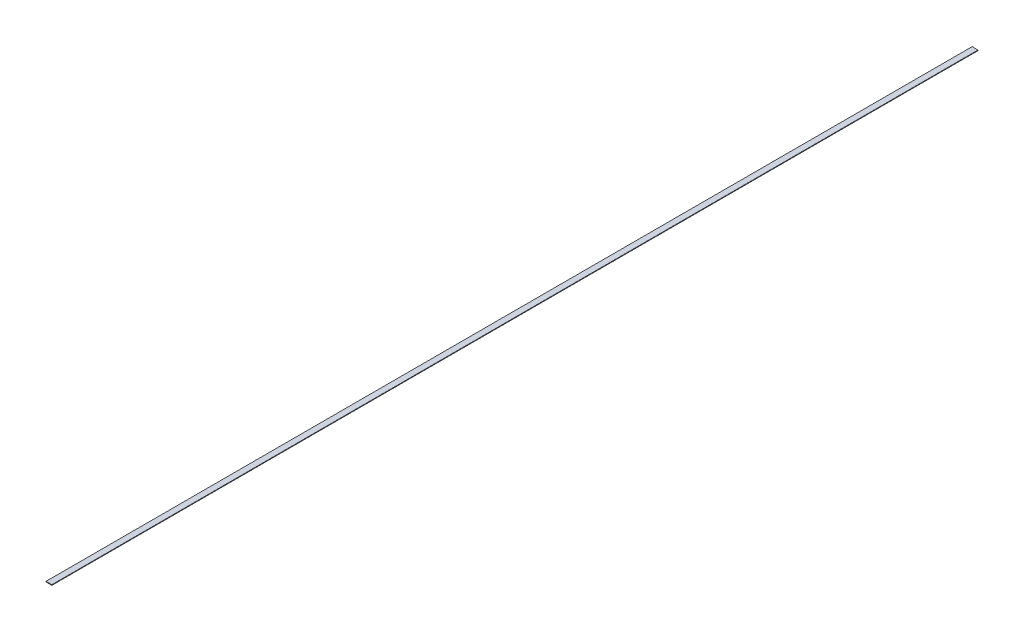
SolidWorks part; units mm, degrees
ref_plane "Front Plane" through (0, 0, 0) normal (0, 0, 1) x (1, 0, 0)
ref_plane "Top Plane" through (0, 0, 0) normal (0, 1, 0) x (1, 0, 0)
ref_plane "Right Plane" through (0, 0, 0) normal (1, 0, 0) x (0, 0, -1)
sketch "Sketch1" plane through (0, 0, 0) normal (0, 1, 0) x (1, 0, 0)
  line L1 (0, 0) -> (50.8, 0)
  line L2 (0, 0) -> (0, 8051.8)
  line L3 (0, 8051.8) -> (50.8, 8051.8)
  line L4 (50.8, 0) -> (50.8, 8051.8)
  dimension "D1" = 50.8
  dimension "D2" = 8051.8
extrude "Boss-Extrude1" add sketch "Sketch1" along normal blind 5.08
